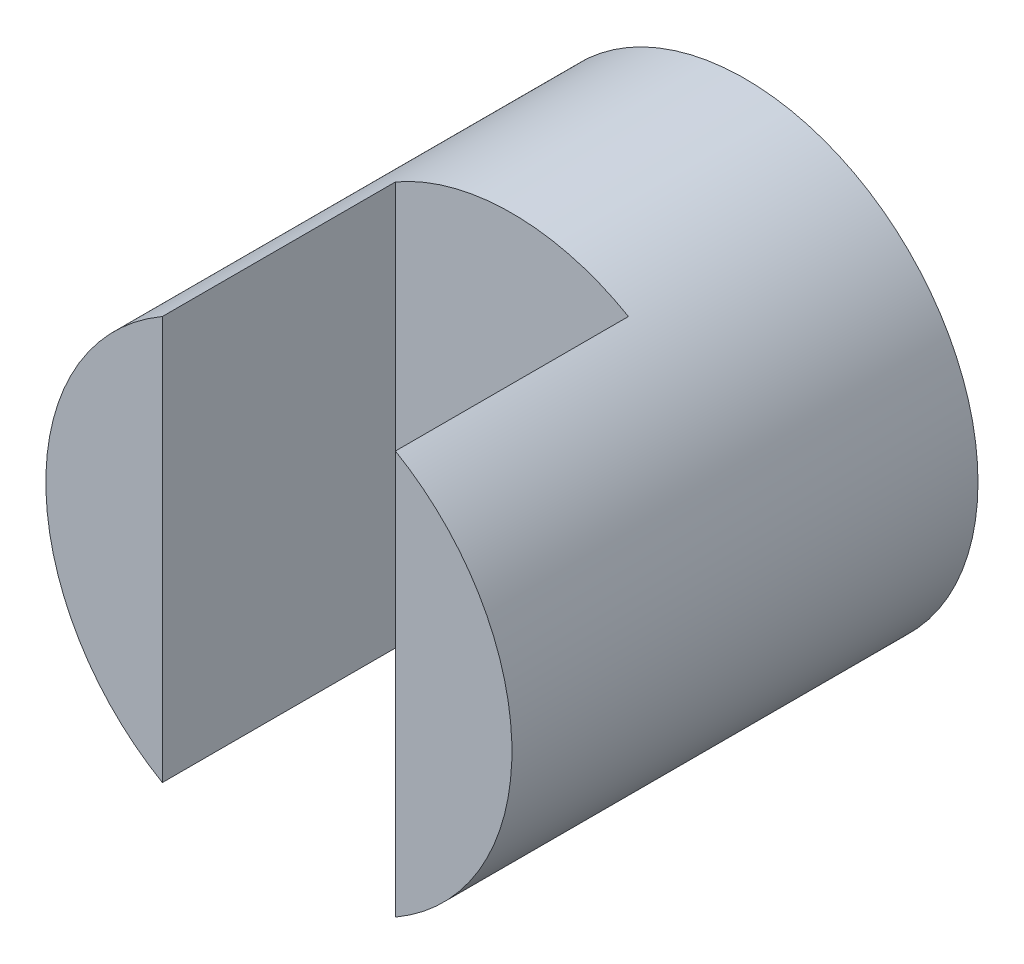
SolidWorks part; units mm, degrees
ref_plane "Front" through (0, 0, 0) normal (0, 0, 1) x (1, 0, 0)
ref_plane "Top" through (0, 0, 0) normal (0, 1, 0) x (1, 0, 0)
ref_plane "Right" through (0, 0, 0) normal (1, 0, 0) x (0, 0, -1)
sketch "Sketch1" plane through (0, 0, 0) normal (0, 0, 1) x (1, 0, 0)
  circle A0 centre (0, 0) radius 2
  dimension "D1" = 4
extrude "Boss-Extrude1" add sketch "Sketch1" along normal blind 4
sketch "Sketch2" plane through (0, 0, 0) normal (0, 1, 0) x (1, 0, 0)
  line L0 (-2, -4) -> (2, -4) construction
  line L1 (-1, -6) -> (1, -6)
  line L2 (-1, -6) -> (-1, -2)
  line L3 (-1, -2) -> (1, -2)
  line L4 (1, -6) -> (1, -2)
  line L5 (-1, -6) -> (1, -2) construction
  line L6 (-1, -2) -> (1, -6) construction
  point P0 (0, -4)
  dimension "D1" = 2
  dimension "D2" = 4
extrude "Cut-Extrude1" cut sketch "Sketch2" against normal mid plane 4
